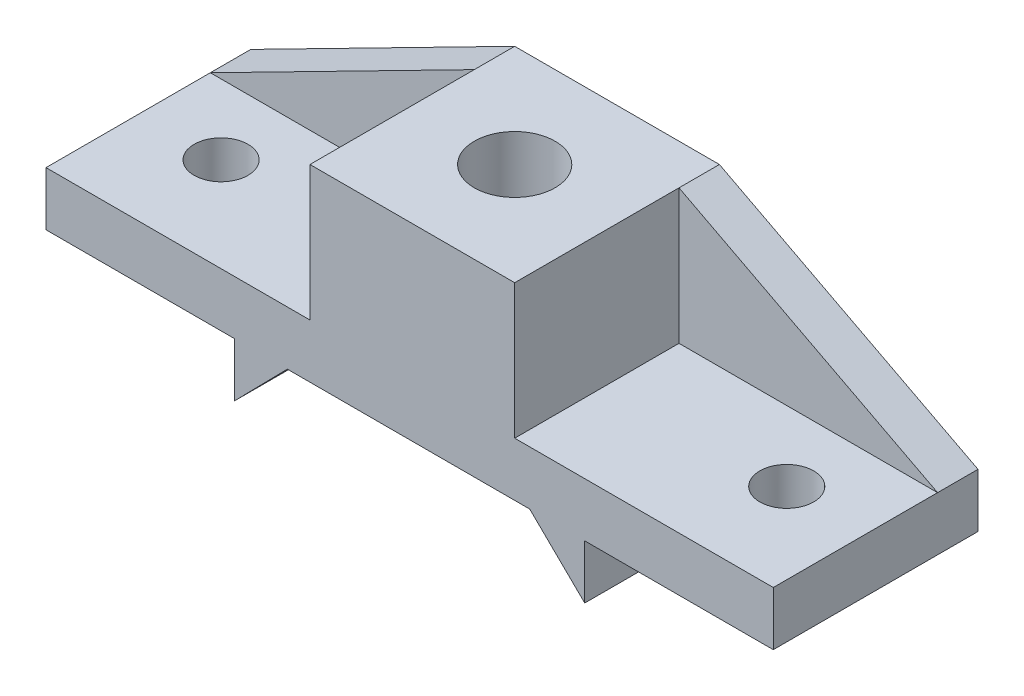
SolidWorks part; units mm, degrees
ref_plane "Front Plane" through (0, 0, 0) normal (0, 0, 1) x (1, 0, 0)
ref_plane "Top Plane" through (0, 0, 0) normal (0, 1, 0) x (1, 0, 0)
ref_plane "Right Plane" through (0, 0, 0) normal (1, 0, 0) x (0, 0, -1)
sketch "Sketch2" plane through (0, 0, 0) normal (0, 0, 1) x (1, 0, 0)
  line L0 (964.2479, 2588.5554) -> (7017.9355, 2588.5554) construction
  line L1 (155.9846, -34.8154) -> (57.9846, -84.8154)
  line L2 (57.9846, -84.8154) -> (57.9846, -104.8154)
  line L3 (57.9846, -104.8154) -> (127.9846, -104.8154)
  line L4 (127.9846, -104.8154) -> (127.9846, -124.8154)
  line L5 (127.9846, -124.8154) -> (147.5846, -104.8154)
  line L6 (147.5846, -104.8154) -> (237.5764, -104.8154)
  line L7 (237.5764, -104.8154) -> (257.9846, -124.8154)
  line L8 (257.9846, -124.8154) -> (257.9846, -104.8154)
  line L9 (257.9846, -104.8154) -> (327.9846, -104.8154)
  line L10 (327.9846, -104.8154) -> (327.9846, -84.8154)
  line L11 (327.9846, -84.8154) -> (231.9846, -34.8154)
  line L12 (231.9846, -34.8154) -> (155.9846, -34.8154)
  point P4 (0, 0)
  point P15 (0, 0)
  dimension "D1" = 76
  dimension "D2" = 20
  dimension "D3" = 70
  dimension "D4" = 70
  dimension "D5" = 130
  dimension "D6" = 20
  dimension "D7" = 20
  dimension "D8" = 20
  dimension "D9" = 20
  dimension "D10" = 20
  dimension "D11" = 70
extrude "Boss-Extrude1" add sketch "Sketch2" along normal blind 76
sketch "Sketch5" plane through (0, 0, 76) normal (0, 0, 1) x (1, 0, 0)
  line L0 (155.9846, -34.8154) -> (155.9846, -84.8154)
  line L1 (155.9846, -84.8154) -> (57.9846, -84.8154)
  line L2 (57.9846, -84.8154) -> (155.9846, -34.8154)
  line L3 (231.9846, -34.8154) -> (231.9846, -84.8154)
  line L4 (231.9846, -84.8154) -> (327.9846, -84.8154)
  line L5 (327.9846, -84.8154) -> (231.9846, -34.8154)
  point P7 (0, 0)
  point P11 (0, 0)
  dimension "D1" = 76
extrude "Cut-Extrude1" cut sketch "Sketch5" against normal blind 61
sketch "Sketch7" plane through (0, -104.8154, 0) normal (0, 1, 0) x (1, 0, 0)
  line L0 (-55, 0) -> (55, 0) construction
  line L1 (57.9846, -15) -> (155.9846, -15) construction
  line L2 (57.9846, -15) -> (57.9846, -76) construction
  line L3 (57.9846, -76) -> (155.9846, -76) construction
  line L4 (155.9846, -15) -> (155.9846, -76) construction
  line L5 (155.9846, -76) -> (231.9846, -76) construction
  line L6 (155.9846, -76) -> (155.9846, 0) construction
  line L7 (155.9846, 0) -> (231.9846, 0) construction
  line L8 (231.9846, -76) -> (231.9846, 0) construction
  line L9 (231.9846, -15) -> (231.9846, 0) construction
  line L11 (327.9846, -76) -> (231.9846, -76) construction
  line L12 (327.9846, -76) -> (327.9846, -15) construction
  line L13 (327.9846, -15) -> (231.9846, -15) construction
  line L14 (231.9846, -76) -> (231.9846, -15) construction
  line L17 (193.9846, 0) -> (193.9846, -76) construction
  line L19 (231.9846, -38) -> (155.9846, -38) construction
  circle A0 centre (193.9846, -38) radius 15
  circle A2 centre (87.9846, -41) radius 10
  circle A3 centre (297.9846, -41) radius 10
  dimension "D1" = 38
  dimension "D2" = 38
  dimension "D3" = 30
  dimension "D4" = 35
  dimension "D5" = 30
  dimension "D6" = 35
extrude "Cut-Extrude4" cut sketch "Sketch7" along normal through all
